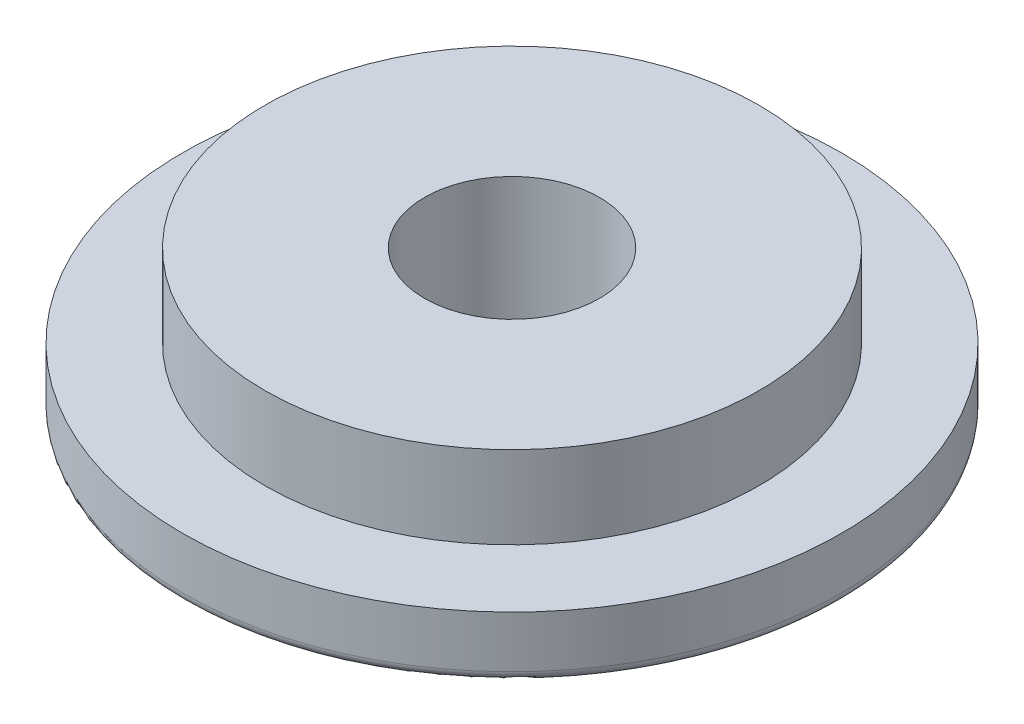
SolidWorks part; units mm, degrees
material "Aluminum Bronze"
ref_plane "Front" through (0, 0, 0) normal (0, 0, 1) x (1, 0, 0)
ref_plane "Top" through (0, 0, 0) normal (0, 1, 0) x (1, 0, 0)
ref_plane "Right" through (0, 0, 0) normal (1, 0, 0) x (0, 0, -1)
sketch "Sketch1" plane through (0, 0, 0) normal (0, 0, 1) x (1, 0, 0)
  line L0 (0, 140.2143) -> (0, -159.7791) construction
  line L1 (-173.1188, 0) -> (195.0551, 0) construction
  line L2 (0, 0) -> (0, 11.1252)
  line L3 (0, 11.1252) -> (19.05, 11.1252)
  line L4 (19.05, 11.1252) -> (19.05, 4.7752)
  line L5 (19.05, 4.7752) -> (25.4, 4.7752)
  line L6 (25.4, 4.7752) -> (25.4, 0.7938)
  line L7 (24.6063, 0) -> (0, 0)
  arc A0 (24.6063, 0) -> (25.4, 0.7938) centre (24.6063, 0.7937) ccw
  point P13 (25.4, 0)
  dimension "D5" = 0.7937
  dimension "D1" = 11.1252
  dimension "D2" = 4.7752
  dimension "D3" = 38.1
  dimension "D4" = 50.8
revolve "Revolve1" add sketch "Sketch1" angle 360 about L0
sketch "Sketch2" plane through (0, 11.1252, 0) normal (0, 1, 0) x (1, 0, 0)
  circle A0 centre (0, 0) radius 6.7469
  dimension "D1" = 13.4937
extrude "Cut-Extrude1" cut sketch "Sketch2" against normal through all
